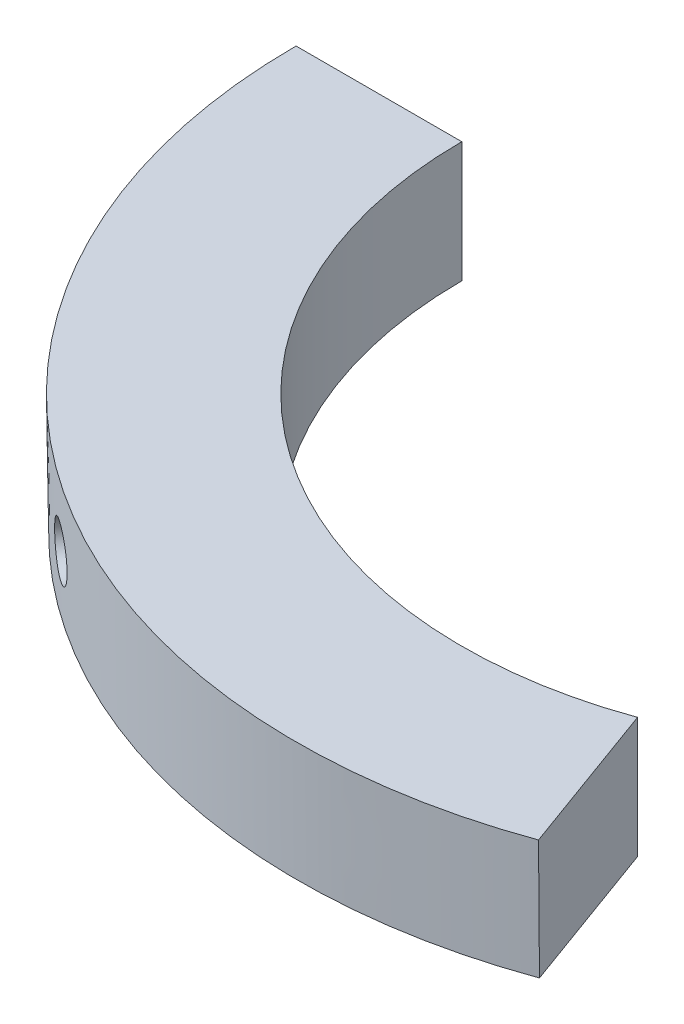
SolidWorks part; units mm, degrees
ref_plane "Front Plane" through (0, 0, 0) normal (0, 0, 1) x (1, 0, 0)
ref_plane "Top Plane" through (0, 0, 0) normal (0, 1, 0) x (1, 0, 0)
ref_plane "Right Plane" through (0, 0, 0) normal (1, 0, 0) x (0, 0, -1)
sketch "Sketch1" plane through (0, 0, 0) normal (0, 0, 1) x (1, 0, 0)
  line L0 (0, 0) -> (0, 8) construction
  line L2 (-29, 0) -> (-29, 8)
  line L3 (-29, 8) -> (-40, 8)
  line L4 (-40, 8) -> (-39.8964, 0.0007)
  line L5 (-39.8964, 0.0007) -> (-29, 0)
revolve "Revolve1" add sketch "Sketch1" angle 110 about L0
hole_wizard "CSK for M3 Countersunk Flat Head Screw1" positions "3DSketch2" profile "Sketch12" countersink size "M3" standard "DIN" end condition through all
sketch3d "3DSketch2"
  point P0 (-16.6932, 3.7995, 23.7136)
sketch "Sketch12" plane through (-16.6932, 3.7995, 23.7136) normal (0, 1, 0) x (-0.8177, 0, -0.5756)
  line L0 (0, 0) -> (0, 26.7336)
  line L1 (0, 26.7336) -> (1.7, 26.7336)
  line L2 (1.7, 26.7336) -> (1.7, 1.45)
  line L3 (1.7, 1.45) -> (3.15, 0)
  line L5 (3.15, 0) -> (0, 0)
  line L6 (-1.7, 1.45) -> (-3.15, 0) construction
  line L11 (0, -6.35) -> (0, 107.95) construction
  dimension "Thru Hole Dia." = 3.4
  dimension "Thru Hole Depth" = 26.7336
  dimension "Near C'Sink Dia." = 6.3
  dimension "Near C'Sink Angle" = 90
